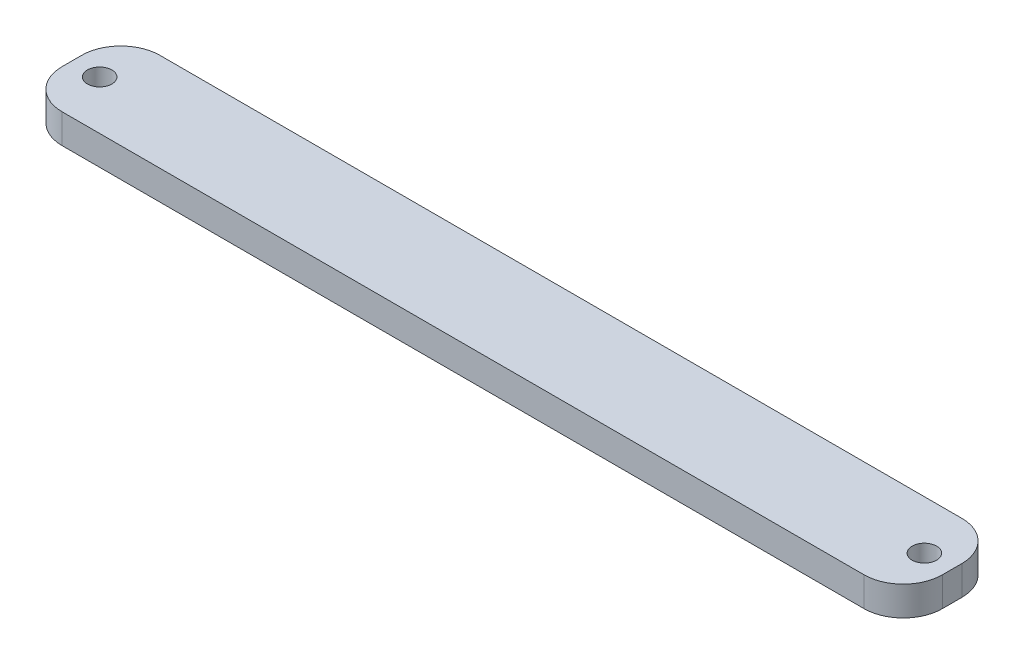
SolidWorks part; units mm, degrees
ref_plane "Front Plane" through (0, 0, 0) normal (0, 0, 1) x (1, 0, 0)
ref_plane "Top Plane" through (0, 0, 0) normal (0, 1, 0) x (1, 0, 0)
ref_plane "Right Plane" through (0, 0, 0) normal (1, 0, 0) x (0, 0, -1)
sketch "Sketch1" plane through (0, 0, 0) normal (0, 1, 0) x (1, 0, 0)
  line L0 (-57.15, 0) -> (57.15, 0)
  point P4 (0, 0)
extrude "Extrude-Thin1" add sketch "Sketch1" along normal blind 3.81 thin contours L0
sketch "Sketch3" plane through (0, 3.81, 0) normal (0, 1, 0) x (1, 0, 0)
  circle A0 centre (53.5469, -6.35) radius 1.5875
fillet "Fillet1" radius 5.08 4 edges at (-57.15, 1.905, 0) (-57.15, 1.905, 12.7) (57.15, 1.905, 12.7) (57.15, 1.905, 0)
extrude "Cut-Extrude1" cut sketch "Sketch3" along direction (0, -1, 0) on the side against the normal blind 3.81 contours A0
mirror "Mirror1" about plane through (0, 0, 0) normal (1, 0, 0) of "Cut-Extrude1"
